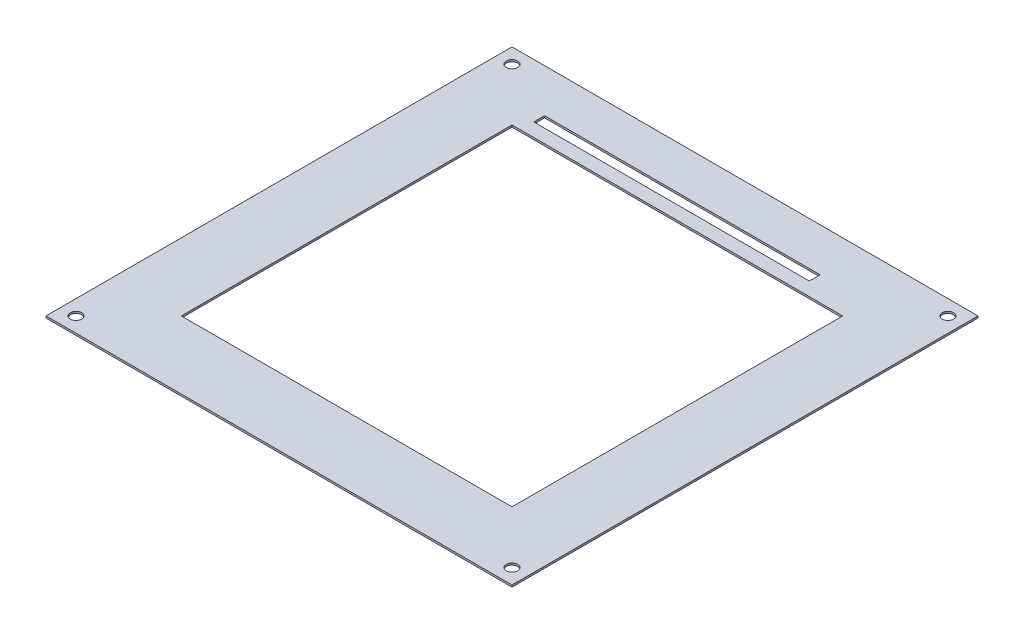
SolidWorks part; units mm, degrees
ref_plane "Спереди" through (0, 0, 0) normal (0, 0, 1) x (1, 0, 0)
ref_plane "Сверху" through (0, 0, 0) normal (0, 1, 0) x (1, 0, 0)
ref_plane "Справа" through (0, 0, 0) normal (1, 0, 0) x (0, 0, -1)
sketch "Эскиз1" plane through (0, 0, 0) normal (0, 1, 0) x (1, 0, 0)
  line L1 (0, 0) -> (124, 0)
  line L2 (0, 0) -> (0, 124)
  line L3 (0, 124) -> (124, 124)
  line L4 (124, 0) -> (124, 124)
  line L5 (18, 106) -> (106, 106)
  line L6 (18, 106) -> (18, 18)
  line L7 (18, 18) -> (106, 18)
  line L8 (106, 106) -> (106, 18)
  line L9 (20.1899, 112.4673) -> (93.5219, 112.4673)
  line L10 (20.1899, 112.4673) -> (20.1899, 109.5967)
  line L11 (20.1899, 109.5967) -> (93.5219, 109.5967)
  line L12 (93.5219, 112.4673) -> (93.5219, 109.5967)
  circle A0 centre (4, 120) radius 1.5
  circle A1 centre (120, 120) radius 1.5
  circle A2 centre (120, 4) radius 1.5
  circle A3 centre (4, 4) radius 1.5
  dimension "D7" = 3
  dimension "D8" = 3
  dimension "D9" = 3
  dimension "D10" = 3
  dimension "D1" = 124
  dimension "D2" = 124
  dimension "D3" = 18
  dimension "D4" = 18
  dimension "D5" = 18
  dimension "D6" = 18
  dimension "D11" = 4
  dimension "D12" = 4
  dimension "D13" = 4
  dimension "D14" = 4
  dimension "D15" = 4
  dimension "D16" = 4
  dimension "D17" = 4
  dimension "D18" = 4
extrude "Бобышка-Вытянуть1" add sketch "Эскиз1" along normal blind 0.5
